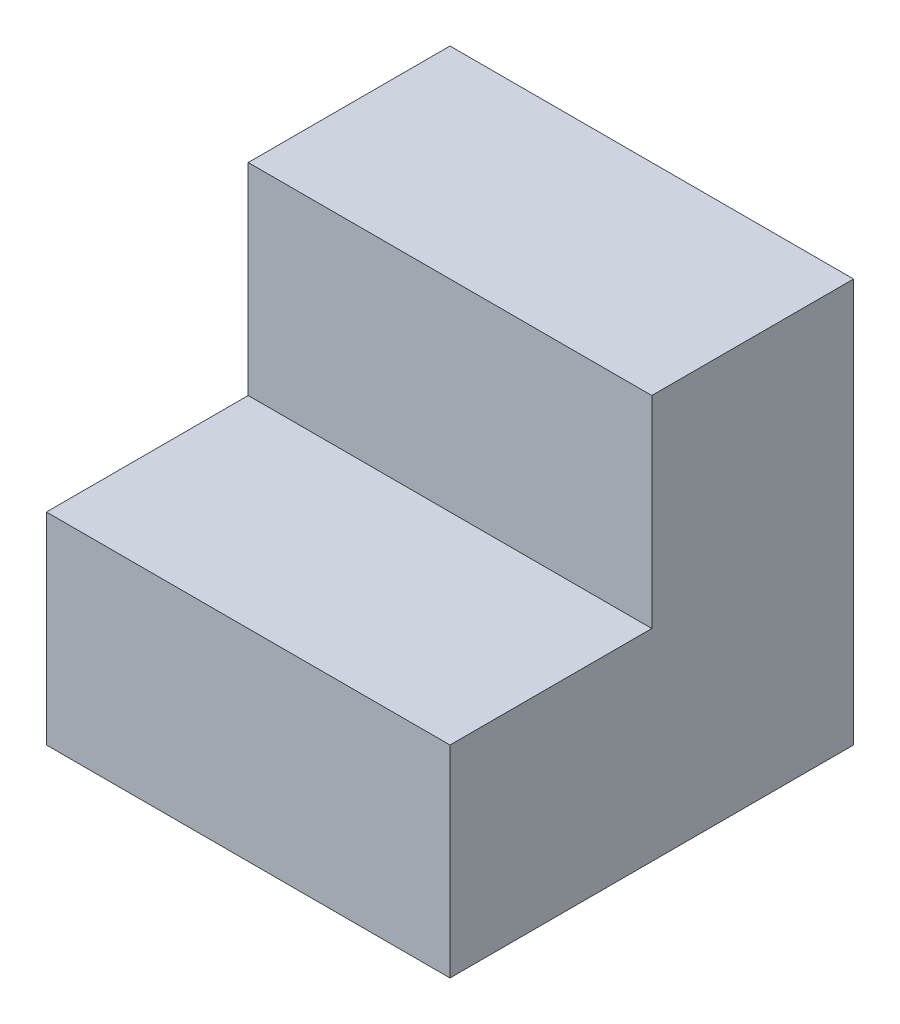
SolidWorks part; units mm, degrees
ref_plane "Ebene vorne" through (0, 0, 0) normal (0, 0, 1) x (1, 0, 0)
ref_plane "Ebene oben" through (0, 0, 0) normal (0, 1, 0) x (1, 0, 0)
ref_plane "Ebene rechts" through (0, 0, 0) normal (1, 0, 0) x (0, 0, -1)
sketch "Skizze1" plane through (0, 0, 0) normal (1, 0, 0) x (0, 0, -1)
  line L0 (0, 0) -> (0, 0.5)
  line L1 (0, 0.5) -> (0.5, 0.5)
  line L2 (0.5, 0.5) -> (0.5, -0.5)
  line L3 (0.5, -0.5) -> (-0.5, -0.5)
  line L4 (-0.5, -0.5) -> (-0.5, 0)
  line L5 (-0.5, 0) -> (0, 0)
  line L6 (0.5, 0) -> (0, 0) construction
  line L7 (0, -0.5) -> (0, 0) construction
  dimension "D1" = 1
extrude "Aufsatz-Linear austragen1" add sketch "Skizze1" along normal mid plane 1
